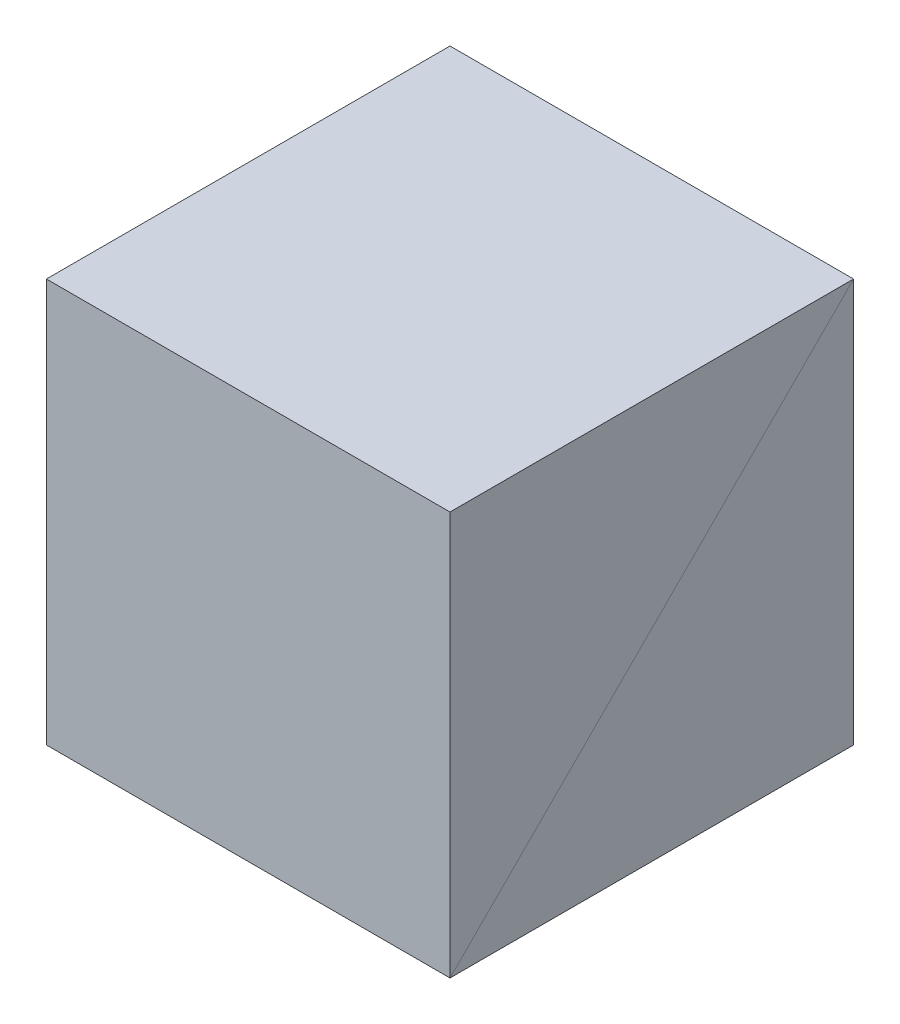
SolidWorks part; units mm, degrees
other "COLL.BOX-Boss-Extrude2"
ref_plane "Piano frontale" through (0, 0, 0) normal (0, 0, 1) x (1, 0, 0)
ref_plane "Piano superiore" through (0, 0, 0) normal (0, 1, 0) x (1, 0, 0)
ref_plane "Piano destro" through (0, 0, 0) normal (1, 0, 0) x (0, 0, -1)
sketch "Sketch1" plane through (0, 0, 0) normal (0, 1, 0) x (1, 0, 0)
  line L1 (-100, -100) -> (100, -100)
  line L2 (-100, -100) -> (-100, 100)
  line L3 (-100, 100) -> (100, 100)
  line L4 (100, -100) -> (100, 100)
  line L5 (-100, -100) -> (100, 100) construction
  line L6 (-100, 100) -> (100, -100) construction
  point P0 (0, 0)
  dimension "D1" = 200
  dimension "D2" = 200
extrude "Boss-Extrude1" add sketch "Sketch1" along normal blind 200
sketch "Sketch2" plane through (0, 200, 0) normal (0, 1, 0) x (1, 0, 0)
  line L4 (100, -100) -> (100, 100)
  line L5 (100, 100) -> (-100, 100)
  line L6 (-100, 100) -> (-100, -100)
  line L7 (-100, -100) -> (100, -100)
  line L8 (100, -100) -> (100, 100)
  line L9 (100, 100) -> (-100, 100)
  line L10 (-100, 100) -> (-100, -100)
  line L11 (-100, -100) -> (100, -100)
  dimension "D1" = 0
extrude "Boss-Extrude2" add sketch "Sketch2" against normal up to surface (200 mm away) separate body up to face at (0, 0, 0)
